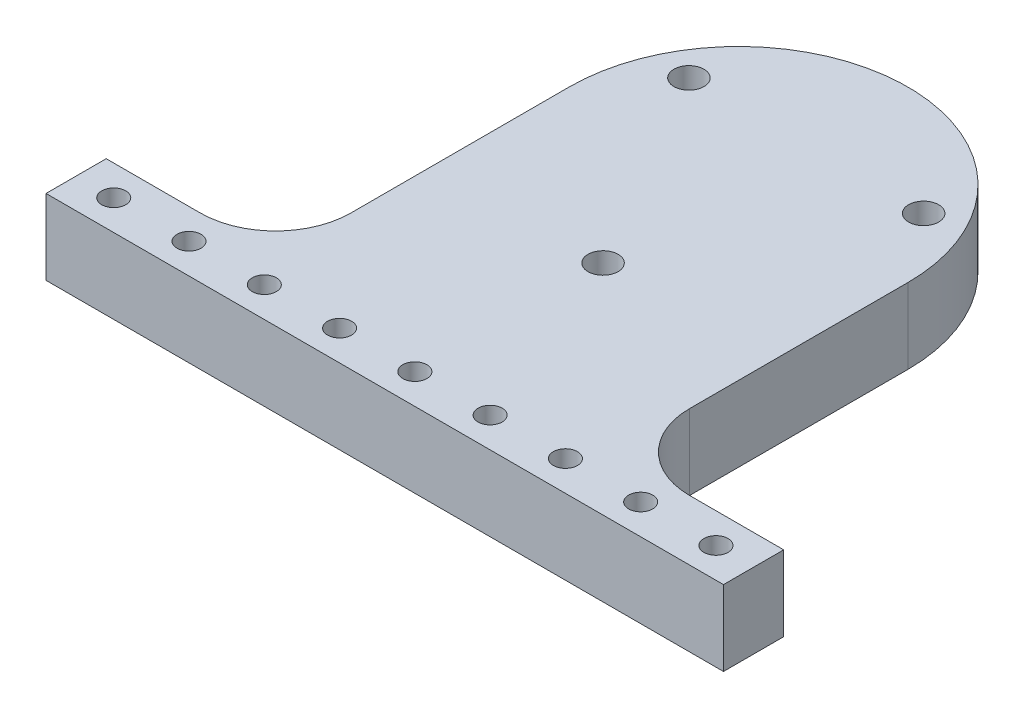
SolidWorks part; units mm, degrees
ref_plane "Front Plane" through (0, 0, 0) normal (0, 0, 1) x (1, 0, 0)
ref_plane "Top Plane" through (0, 0, 0) normal (0, 1, 0) x (1, 0, 0)
ref_plane "Right Plane" through (0, 0, 0) normal (1, 0, 0) x (0, 0, -1)
sketch "Sketch1" plane through (0, 0, 0) normal (0, 1, 0) x (1, 0, 0)
  line L1 (-45, -4) -> (45, -4)
  line L2 (-45, -4) -> (-45, 4)
  line L3 (-45, 4) -> (45, 4)
  line L4 (45, -4) -> (45, 4)
  line L5 (-45, -4) -> (45, 4) construction
  line L6 (-45, 4) -> (45, -4) construction
  point P0 (0, 0)
  dimension "D1" = 8
  dimension "D2" = 90
extrude "Boss-Extrude1" add sketch "Sketch1" along normal blind 10
sketch "Sketch2" plane through (0, 0, 0) normal (0, 1, 0) x (1, 0, 0)
  line L0 (-15.5885, 52.0001) -> (15.5885, 52.0001) construction
  line L1 (15.5885, 52.0001) -> (0, 25) construction
  line L2 (0, 25) -> (-15.5885, 52.0001) construction
  line L3 (45, -4) -> (45, 4) construction
  line L4 (-45, -4) -> (45, -4) construction
  circle A0 centre (0, 25) radius 2
  circle A1 centre (-15.5885, 52.0001) radius 2
  circle A2 centre (15.5885, 52.0001) radius 2
  dimension "D3" = 4
  dimension "D1" = 45
  dimension "D2" = 29
  dimension "D4" = 31.177
sketch "Sketch3" plane through (0, 0, 0) normal (0, 1, 0) x (1, 0, 0)
  line L0 (-15.5885, 52.0001) -> (7.7942, 38.5) construction
  line L1 (15.5885, 52.0001) -> (0, 25) construction
  line L2 (15.5885, 52.0001) -> (-7.7942, 38.5) construction
  line L3 (0, 25) -> (-15.5885, 52.0001) construction
  line L4 (-22.5, 43) -> (-22.5, 4)
  line L5 (45, 4) -> (-45, 4) construction
  line L6 (-22.5, 4) -> (22.5, 4)
  line L7 (22.5, 4) -> (22.5, 43)
  arc A0 (22.5, 43) -> (-22.5, 43) centre (0, 43) ccw
  point P10 (0, 43)
  dimension "D1" = 45
extrude "Boss-Extrude2" add sketch "Sketch3" along normal up to surface (10 mm away) up to face at (0, 10, 0)
sketch "Sketch4" plane through (0, 10, 0) normal (0, 1, 0) x (1, 0, 0)
  circle A0 centre (-15.5885, 52.0001) radius 2
  circle A1 centre (15.5885, 52.0001) radius 2
  circle A2 centre (0, 25) radius 2
  dimension "D1" = 4
extrude "Cut-Extrude1" cut sketch "Sketch4" against normal through all
fillet "Fillet1" radius 10 2 edges at (22.5, 5, -4) (-22.5, 5, -4)
sketch "Sketch5" plane through (0, 10, 0) normal (0, 1, 0) x (1, 0, 0)
  line L0 (-45, 4) -> (-45, -4) construction
  circle A0 centre (-40, 0) radius 1.6
  point P2 (0, 0)
  dimension "D2" = 3.2
  dimension "D1" = 5
extrude "Cut-Extrude2" cut sketch "Sketch5" against normal through all
pattern_linear "LPattern1" count 10 spacing 10 along (1, 0, 0) of "Cut-Extrude2"
